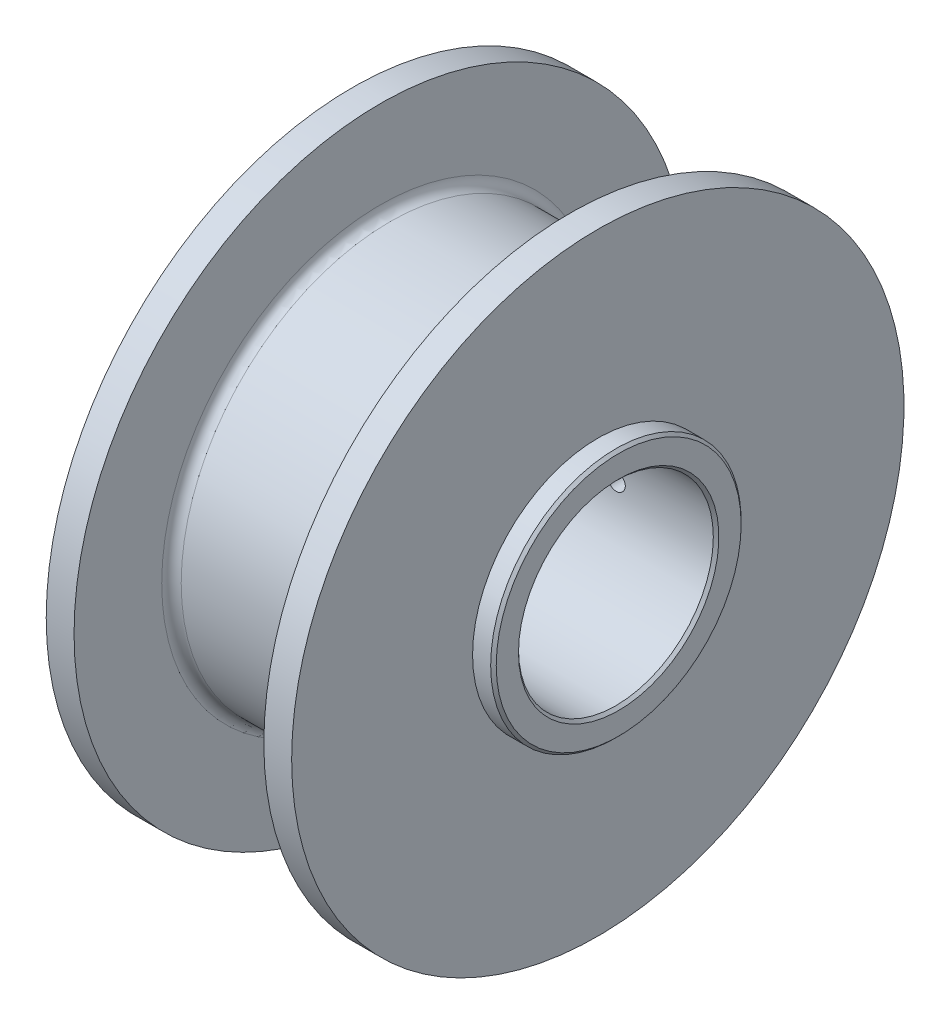
SolidWorks part; units mm, degrees
ref_plane "Front Plane" through (0, 0, 0) normal (0, 0, 1) x (1, 0, 0)
ref_plane "Top Plane" through (0, 0, 0) normal (0, 1, 0) x (1, 0, 0)
ref_plane "Right Plane" through (0, 0, 0) normal (1, 0, 0) x (0, 0, -1)
sketch "Sketch1" plane through (0, 0, 0) normal (0, 0, 1) x (1, 0, 0)
  line L0 (3.81, 55.88) -> (8.89, 55.88)
  line L1 (8.89, 55.88) -> (8.89, 38.1)
  line L3 (43.528, 38.1) -> (43.528, 55.88)
  line L4 (43.528, 55.88) -> (48.608, 55.88)
  line L5 (48.608, 55.88) -> (48.608, 22.86)
  line L6 (48.608, 22.86) -> (52.418, 22.86)
  line L7 (52.418, 22.86) -> (52.418, 17.78)
  line L8 (52.418, 17.78) -> (15.08, 17.78)
  line L9 (15.08, 17.78) -> (15.08, 16.002)
  line L10 (15.08, 16.002) -> (5.08, 16.002)
  line L11 (5.08, 16.002) -> (5.08, 11.08)
  line L12 (5.08, 11.08) -> (0, 11.08)
  line L13 (0, 11.08) -> (0, 22.86)
  line L14 (0, 22.86) -> (3.81, 22.86)
  line L15 (3.81, 22.86) -> (3.81, 55.88)
  line L16 (0, 0) -> (18.9296, 0) construction
  line L18 (8.89, 38.1) -> (43.528, 38.1)
  point P19 (9.4648, 0)
  dimension "D2" = 10
  dimension "D3" = 37.338
  dimension "D1" = 16.002
  dimension "D5" = 17.78
  dimension "D6" = 22.86
  dimension "D7" = 22.86
  dimension "D8" = 5.08
  dimension "D9" = 55.88
  dimension "D10" = 55.88
  dimension "D14" = 3.81
  dimension "D15" = 3.81
  dimension "D16" = 5.08
  dimension "D11" = 38.1
  dimension "D12" = 11.08
revolve "Revolve1" add sketch "Sketch1" angle 360 about L16
ref_plane "Plane1" through (34.257, 0, 0) normal (1, 0, 0) x (0, 0, -1)
sketch "Sketch2" plane through (34.257, 0, 0) normal (1, 0, 0) x (0, 0, -1)
  point P0 (0, 0)
ref_plane "Plane2" through (0, 0, -38.1) normal (0, 0, -1) x (-1, 0, 0)
sketch "Sketch3" plane through (0, 0, -38.1) normal (0, 0, -1) x (-1, 0, 0)
  line L0 (0, 0) -> (-24.097, 0) construction
  line L1 (-44.417, 25.4) -> (-24.097, 25.4)
  line L2 (-44.417, 25.4) -> (-44.417, -25.4)
  line L3 (-44.417, -25.4) -> (-24.097, -25.4)
  line L4 (-24.097, 25.4) -> (-24.097, -25.4)
  line L5 (-34.257, 0) -> (-34.257, 25.4) construction
  point P4 (0, 0)
  point P8 (-34.257, 0)
  dimension "D1" = 50.8
  dimension "D2" = 20.32
extrude "Cut-Extrude1" cut sketch "Sketch3" against normal blind 2.54
sketch "Sketch4" plane through (0, 0, -38.1) normal (0, 0, -1) x (-1, 0, 0)
  point P0 (-34.257, 0)
hole_wizard "1/8 (0.125) Diameter Hole1" positions "Sketch4" profile "Sketch5" hole size "1/8" standard "ANSI Inch"
sketch "Sketch5" plane through (34.257, 0, -38.1) normal (1, 0, 0) x (0, 1, 0)
  line L0 (0, 0) -> (0, 20.32)
  line L1 (0, 20.32) -> (1.5875, 20.32)
  line L2 (1.5875, 20.32) -> (1.5875, 0)
  line L5 (1.5875, 0) -> (0, 0)
  line L11 (0, -6.35) -> (0, 107.95) construction
  dimension "Thru Hole Dia." = 3.175
  dimension "Thru Hole Depth" = 20.32
fillet "Fillet2" radius 1.778 2 edges at (8.89, 0, 38.1) (43.528, 0, 38.1)
chamfer "Chamfer1" distance 0.508 4 edges at (0, 0, 22.86) (52.418, 0, 22.86) (52.418, 0, 17.78) (0, 0, 11.08)
equation "\"bearing_radius\"= 0.629921"
equation "\"bearing_width\"=0.393701"
equation "\"D2@Sketch1\"=\"bearing_width\""
equation "\"kero_radius\"=0.23622in"
equation "\"lox_radius\"=0.23622in"
equation "\"Cavity_width\"=0.031in"
equation "\"tooth_width\"=0.01in"
equation "\"cavity_depth\"=0.031in"
equation "\"seal_step\"=0.01in"
equation "\"purge_length\"=0.04in"
equation "\"insert_radius\"= 0.7in"
equation "\"recycle_groove width\"= 0.06in"
equation "\"recycle_groove_depth\"= 0.06in"
equation "\"N2_purge_width\"= .06in"
equation "\"N2_purge_depth\"= .06in"
equation "\"drain_width\"= .06in"
equation "\"drain_depth\"= .06in"
equation "\"radial_clearance\"= .002in"
equation "\"IPS_flange_width\"= .2in"
equation "\"IPS_flange_radius\"= 2.2in"
equation "\"IPS_LOX_male_radius\"= .9in"
equation "\"IPS_Kero_male_radius\"= .9in"
equation "\"IPS_radius\"= 1.5in"
equation "\"D5@Sketch1\"=\"insert_radius\""
equation "\"InsertLength\"= 1.47in"
equation "\"D3@Sketch1\"=\"InsertLength\""
equation "\"D6@Sketch1\"=\"IPS_Kero_male_radius\""
equation "\"D7@Sketch1\"=\"IPS_LOX_male_radius\""
equation "\"D8@Sketch1\"=\"IPS_flange_width\""
equation "\"D9@Sketch1\"=\"IPS_flange_radius\""
equation "\"D10@Sketch1\"=\"IPS_flange_radius\""
equation "\"D12@Sketch1\"=\"lox_radius\"+.2"
equation "\"D11@Sketch1\"=\"IPS_radius\""
